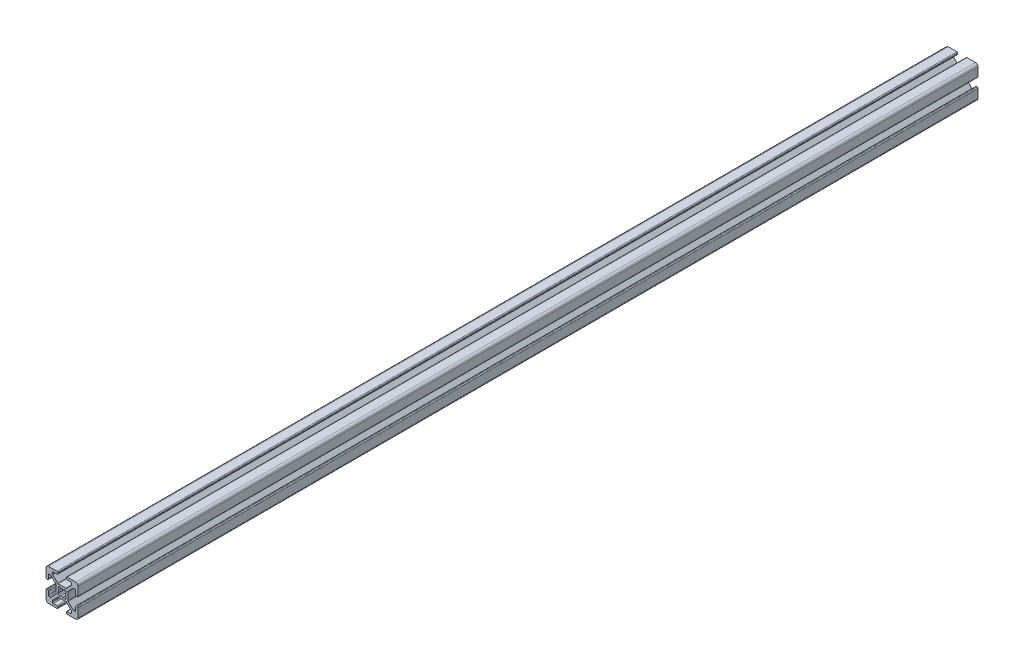
SolidWorks part; units mm, degrees
material "6061-T6 (SS)"
ref_plane "Front Plane" through (0, 0, 0) normal (0, 0, 1) x (1, 0, 0)
ref_plane "Top Plane" through (0, 0, 0) normal (0, 1, 0) x (1, 0, 0)
ref_plane "Right Plane" through (0, 0, 0) normal (1, 0, 0) x (0, 0, -1)
sketch "Sketch1" plane through (0, 0, 0) normal (0, 1, 0) x (1, 0, 0)
  line L0 (0, 0) -> (0, 560)
  dimension "D1" = 560
other "Metric al extrusion 20-2020 PROFILE(1)"
ref_plane "Plane1" through (0, 0, 0) normal (0, 0, -1) x (-1, 0, 0)
sketch "Sketch19" plane through (0, 0, 0) normal (0, 0, -1) x (-1, 0, 0)
  line L0 (9.8952, 3.5708) -> (9.4112, 3.5708)
  line L1 (8.9032, 4.0788) -> (8.9032, 6.4278)
  line L2 (10.4032, 4.0788) -> (10.4032, 9.4408)
  line L3 (4.0582, -1.4431) -> (4.0582, 3.3247)
  line L4 (7.6693, 6.9358) -> (8.3952, 6.9358)
  line L5 (7.3101, 6.787) -> (4.207, 3.6839)
  line L6 (9.8952, -1.6892) -> (9.4112, -1.6892)
  line L7 (10.4032, -2.1972) -> (10.4032, -7.5592)
  line L8 (8.9032, -2.1972) -> (8.9032, -4.5462)
  line L9 (7.6693, -5.0542) -> (8.3952, -5.0542)
  line L10 (7.3101, -4.9054) -> (4.207, -1.8023)
  line L11 (2.5281, -1.3637) -> (2.7077, -1.1841)
  line L12 (-2.2268, 10.4328) -> (-2.2268, 9.9488)
  line L13 (-2.7348, 10.9408) -> (-8.0968, 10.9408)
  line L14 (-2.7348, 9.4408) -> (-5.0838, 9.4408)
  line L15 (2.7871, 4.5958) -> (-1.9807, 4.5958)
  line L16 (-5.5918, 8.2069) -> (-5.5918, 8.9328)
  line L17 (-5.443, 7.8477) -> (-2.3399, 4.7446)
  line L18 (3.0332, 10.4328) -> (3.0332, 9.9488)
  line L19 (3.5412, 10.9408) -> (8.9032, 10.9408)
  line L20 (3.5412, 9.4408) -> (5.8902, 9.4408)
  line L21 (6.3982, 8.2069) -> (6.3982, 8.9328)
  line L22 (6.2494, 7.8477) -> (3.1463, 4.7446)
  line L23 (2.7077, 3.0657) -> (2.5281, 3.2453)
  line L24 (-9.0888, -1.6892) -> (-8.6048, -1.6892)
  line L25 (-9.5968, -2.1972) -> (-9.5968, -7.5592)
  line L26 (-8.0968, -2.1972) -> (-8.0968, -4.5462)
  line L27 (-3.2518, 3.3247) -> (-3.2518, -1.4431)
  line L28 (-6.8629, -5.0542) -> (-7.5888, -5.0542)
  line L29 (-6.5037, -4.9054) -> (-3.4006, -1.8023)
  line L30 (-9.0888, 3.5708) -> (-8.6048, 3.5708)
  line L31 (-9.5968, 4.0788) -> (-9.5968, 9.4408)
  line L32 (-8.0968, 4.0788) -> (-8.0968, 6.4278)
  line L33 (-6.8629, 6.9358) -> (-7.5888, 6.9358)
  line L34 (-6.5037, 6.787) -> (-3.4006, 3.6839)
  line L35 (-1.7217, 3.2453) -> (-1.9013, 3.0657)
  line L36 (3.0332, -8.5512) -> (3.0332, -8.0672)
  line L37 (3.5412, -9.0592) -> (8.9032, -9.0592)
  line L38 (3.5412, -7.5592) -> (5.8902, -7.5592)
  line L39 (-1.9807, -2.7142) -> (2.7871, -2.7142)
  line L40 (6.3982, -6.3253) -> (6.3982, -7.0512)
  line L41 (6.2494, -5.9661) -> (3.1463, -2.863)
  line L42 (-2.2268, -8.5512) -> (-2.2268, -8.0672)
  line L43 (-2.7348, -9.0592) -> (-8.0968, -9.0592)
  line L44 (-2.7348, -7.5592) -> (-5.0838, -7.5592)
  line L45 (-5.5918, -6.3253) -> (-5.5918, -7.0512)
  line L46 (-5.443, -5.9661) -> (-2.3399, -2.863)
  line L47 (-1.9013, -1.1841) -> (-1.7217, -1.3637)
  arc A0 (-0.4008, -0.9944) -> (1.2072, -0.9944) centre (0.4032, 0.9408) ccw
  arc A1 (8.9032, 6.4278) -> (8.3952, 6.9358) centre (8.3952, 6.4278) ccw
  arc A2 (7.6693, 6.9358) -> (7.3101, 6.787) centre (7.6693, 6.4278) ccw
  arc A3 (4.207, 3.6839) -> (4.0582, 3.3247) centre (4.5662, 3.3247) ccw
  arc A4 (4.0582, -1.4431) -> (4.207, -1.8023) centre (4.5662, -1.4431) ccw
  arc A5 (7.3101, -4.9054) -> (7.6693, -5.0542) centre (7.6693, -4.5462) ccw
  arc A6 (8.3952, -5.0542) -> (8.9032, -4.5462) centre (8.3952, -4.5462) ccw
  arc A7 (9.4112, -1.6892) -> (8.9032, -2.1972) centre (9.4112, -2.1972) ccw
  arc A8 (10.4032, -2.1972) -> (9.8952, -1.6892) centre (9.8952, -2.1972) ccw
  arc A9 (9.8952, 3.5708) -> (10.4032, 4.0788) centre (9.8952, 4.0788) ccw
  arc A10 (8.9032, 4.0788) -> (9.4112, 3.5708) centre (9.4112, 4.0788) ccw
  arc A11 (1.2072, -0.9944) -> (2.5281, -1.3637) centre (1.9716, -0.8072) ccw
  arc A12 (2.7077, -1.1841) -> (2.3383, 0.1368) centre (2.1512, -0.6276) ccw
  arc A13 (-2.2268, 10.4328) -> (-2.7348, 10.9408) centre (-2.7348, 10.4328) ccw
  arc A14 (-2.7348, 9.4408) -> (-2.2268, 9.9488) centre (-2.7348, 9.9488) ccw
  arc A15 (2.3383, 0.1368) -> (2.3383, 1.7448) centre (0.4032, 0.9408) ccw
  arc A16 (-2.3399, 4.7446) -> (-1.9807, 4.5958) centre (-1.9807, 5.1038) ccw
  arc A17 (-5.0838, 9.4408) -> (-5.5918, 8.9328) centre (-5.0838, 8.9328) ccw
  arc A18 (-5.5918, 8.2069) -> (-5.443, 7.8477) centre (-5.0838, 8.2069) ccw
  arc A19 (3.0332, 9.9488) -> (3.5412, 9.4408) centre (3.5412, 9.9488) ccw
  arc A20 (3.5412, 10.9408) -> (3.0332, 10.4328) centre (3.5412, 10.4328) ccw
  arc A21 (6.3982, 8.9328) -> (5.8902, 9.4408) centre (5.8902, 8.9328) ccw
  arc A22 (6.2494, 7.8477) -> (6.3982, 8.2069) centre (5.8902, 8.2069) ccw
  arc A23 (2.7871, 4.5958) -> (3.1463, 4.7446) centre (2.7871, 5.1038) ccw
  arc A24 (2.3383, 1.7448) -> (2.7077, 3.0657) centre (2.1512, 2.5092) ccw
  arc A25 (2.5281, 3.2453) -> (1.2072, 2.8759) centre (1.9716, 2.6888) ccw
  arc A26 (-9.0888, -1.6892) -> (-9.5968, -2.1972) centre (-9.0888, -2.1972) ccw
  arc A27 (-8.0968, -2.1972) -> (-8.6048, -1.6892) centre (-8.6048, -2.1972) ccw
  arc A28 (1.2072, 2.8759) -> (-0.4008, 2.8759) centre (0.4032, 0.9408) ccw
  arc A29 (-3.4006, -1.8023) -> (-3.2518, -1.4431) centre (-3.7598, -1.4431) ccw
  arc A30 (-8.0968, -4.5462) -> (-7.5888, -5.0542) centre (-7.5888, -4.5462) ccw
  arc A31 (-6.8629, -5.0542) -> (-6.5037, -4.9054) centre (-6.8629, -4.5462) ccw
  arc A32 (-8.6048, 3.5708) -> (-8.0968, 4.0788) centre (-8.6048, 4.0788) ccw
  arc A33 (-9.5968, 4.0788) -> (-9.0888, 3.5708) centre (-9.0888, 4.0788) ccw
  arc A34 (-7.5888, 6.9358) -> (-8.0968, 6.4278) centre (-7.5888, 6.4278) ccw
  arc A35 (-6.5037, 6.787) -> (-6.8629, 6.9358) centre (-6.8629, 6.4278) ccw
  arc A36 (-3.2518, 3.3247) -> (-3.4006, 3.6839) centre (-3.7598, 3.3247) ccw
  arc A37 (-0.4008, 2.8759) -> (-1.7217, 3.2453) centre (-1.1652, 2.6888) ccw
  arc A38 (-1.9013, 3.0657) -> (-1.5319, 1.7448) centre (-1.3448, 2.5092) ccw
  arc A39 (3.0332, -8.5512) -> (3.5412, -9.0592) centre (3.5412, -8.5512) ccw
  arc A40 (3.5412, -7.5592) -> (3.0332, -8.0672) centre (3.5412, -8.0672) ccw
  arc A41 (-1.5319, 1.7448) -> (-1.5319, 0.1368) centre (0.4032, 0.9408) ccw
  arc A42 (3.1463, -2.863) -> (2.7871, -2.7142) centre (2.7871, -3.2222) ccw
  arc A43 (5.8902, -7.5592) -> (6.3982, -7.0512) centre (5.8902, -7.0512) ccw
  arc A44 (6.3982, -6.3253) -> (6.2494, -5.9661) centre (5.8902, -6.3253) ccw
  arc A45 (-2.2268, -8.0672) -> (-2.7348, -7.5592) centre (-2.7348, -8.0672) ccw
  arc A46 (-2.7348, -9.0592) -> (-2.2268, -8.5512) centre (-2.7348, -8.5512) ccw
  arc A47 (-5.5918, -7.0512) -> (-5.0838, -7.5592) centre (-5.0838, -7.0512) ccw
  arc A48 (-5.443, -5.9661) -> (-5.5918, -6.3253) centre (-5.0838, -6.3253) ccw
  arc A49 (-1.9807, -2.7142) -> (-2.3399, -2.863) centre (-1.9807, -3.2222) ccw
  arc A50 (-1.5319, 0.1368) -> (-1.9013, -1.1841) centre (-1.3448, -0.6276) ccw
  arc A51 (-1.7217, -1.3637) -> (-0.4008, -0.9944) centre (-1.1652, -0.8072) ccw
  arc A52 (10.4032, 9.4408) -> (8.9032, 10.9408) centre (8.9032, 9.4408) ccw
  arc A53 (8.9032, -9.0592) -> (10.4032, -7.5592) centre (8.9032, -7.5592) ccw
  arc A54 (-9.5968, -7.5592) -> (-8.0968, -9.0592) centre (-8.0968, -7.5592) ccw
  arc A55 (-8.0968, 10.9408) -> (-9.5968, 9.4408) centre (-8.0968, 9.4408) ccw
  point P157 (0, 0)
